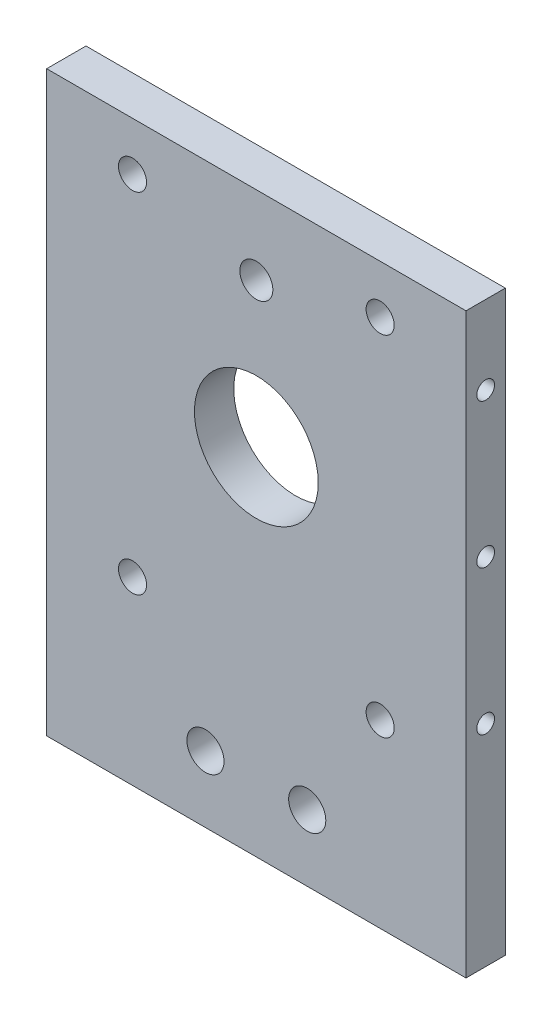
SolidWorks part; units mm, degrees
ref_plane "Alzado" through (0, 0, 0) normal (0, 0, 1) x (1, 0, 0)
ref_plane "Planta" through (0, 0, 0) normal (0, 1, 0) x (1, 0, 0)
ref_plane "Vista lateral" through (0, 0, 0) normal (1, 0, 0) x (0, 0, -1)
sketch "Croquis1" plane through (0, 0, 0) normal (0, 0, 1) x (1, 0, 0)
  line L1 (-50.8, 54) -> (50.8, 54)
  line L2 (-50.8, 54) -> (-50.8, -54)
  line L3 (-50.8, -54) -> (50.8, -54)
  line L4 (50.8, 54) -> (50.8, -54)
  line L5 (-50.8, 54) -> (50.8, -54) construction
  line L6 (-50.8, -54) -> (50.8, 54) construction
  point P0 (0, 0)
  dimension "D1" = 108
  dimension "D2" = 101.6
extrude "Saliente-Extruir1" add sketch "Croquis1" along normal blind 9.525
sketch "Croquis2" plane through (0, 0, 9.525) normal (0, 0, 1) x (1, 0, 0)
  line L0 (50.8, 0) -> (-50.8, 0) construction
  line L1 (50.8, -54) -> (50.8, 54) construction
  line L2 (-50.8, 54) -> (-50.8, -54) construction
  line L3 (-50.8, -54) -> (50.8, -54) construction
  line L4 (-42.5, 54) -> (42.5, 54) construction
  line L5 (-42.5, 54) -> (-42.5, -54) construction
  line L6 (-42.5, -54) -> (42.5, -54) construction
  line L7 (42.5, 54) -> (42.5, -54) construction
  line L8 (-42.5, 54) -> (42.5, -54) construction
  line L9 (-42.5, -54) -> (42.5, 54) construction
  line L10 (-42.5, -35.9) -> (42.5, -35.9) construction
  line L11 (-42.5, -42.25) -> (42.5, -42.25) construction
  line L12 (0, -35.9) -> (0, -54) construction
  line L13 (-30, -42.25) -> (-30, 42.25) construction
  circle A0 centre (0, 0) radius 15
  circle A1 centre (0, -42.25) radius 4 construction
  circle A2 centre (30, -42.25) radius 3.4
  circle A3 centre (-30, -42.25) radius 3.4
  circle A4 centre (30, 42.25) radius 3.4
  circle A5 centre (-30, 42.25) radius 3.4
  circle A6 centre (-30, -15.9) radius 2.5 construction
  circle A7 centre (30, -15.9) radius 2.5 construction
  point P6 (0, 0)
  dimension "D2" = 30
  dimension "D5" = 8
  dimension "D6" = 6.8
  dimension "D10" = 5
  dimension "D1" = 85
  dimension "D3" = 6.35
  dimension "D4" = 42.25
  dimension "D7" = 30
  dimension "D8" = 0
  dimension "D9" = 20
extrude "Cortar-Extruir1" cut sketch "Croquis2" against normal through all
sketch "Croquis3" plane through (-50.8, 0, 0) normal (-1, 0, 0) x (0, 0, 1)
  line L0 (4.7625, 54) -> (4.7625, -54) construction
  line L1 (9.525, 54) -> (0, 54) construction
  line L2 (9.525, -54) -> (0, -54) construction
  line L3 (0, 0) -> (9.525, 0) construction
  line L4 (9.525, 54) -> (9.525, -54) construction
  circle A0 centre (4.7625, 0) radius 2.15
  circle A1 centre (4.7625, -35) radius 2.15
  circle A2 centre (4.7625, 35) radius 2.15
  dimension "D1" = 4.3
  dimension "D2" = 4.3
  dimension "D3" = 35
extrude "Cortar-Extruir2" cut sketch "Croquis3" against normal blind 15
sketch "Croquis4" plane through (50.8, 0, 0) normal (1, 0, 0) x (0, 0, -1)
  line L0 (-4.7625, -54) -> (-4.7625, 54) construction
  line L1 (-9.525, -54) -> (0, -54) construction
  line L2 (-9.525, 54) -> (0, 54) construction
  line L3 (0, 0) -> (-9.525, 0) construction
  line L4 (0, -54) -> (0, 54) construction
  line L5 (-9.525, -54) -> (-9.525, 54) construction
  circle A0 centre (-4.7625, 0) radius 2.15
  circle A1 centre (-4.7625, -35) radius 2.15
  circle A2 centre (-4.7625, 35) radius 2.15
  dimension "D1" = 4.3
  dimension "D2" = 4.3
  dimension "D3" = 35
extrude "Cortar-Extruir3" cut sketch "Croquis4" against normal blind 15
sketch "Croquis5" plane through (0, 0, 9.525) normal (0, 0, 1) x (1, 0, 0)
  line L0 (0, 54) -> (0, 70) construction
  line L1 (50.8, 54) -> (-50.8, 54) construction
  line L2 (-50.8, -54) -> (50.8, -54) construction
  line L3 (-50.8, 86) -> (50.8, 86) construction
  line L4 (-50.8, 86) -> (-50.8, 54) construction
  line L5 (-50.8, 54) -> (50.8, 54) construction
  line L6 (50.8, 86) -> (50.8, 54) construction
  line L7 (-50.8, 86) -> (50.8, 54) construction
  line L8 (-50.8, 54) -> (50.8, 86) construction
  line L9 (0, 0) -> (50.8, 0) construction
  line L10 (50.8, -54) -> (50.8, 54) construction
  line L11 (-50.8, -54) -> (50.8, -54)
  line L12 (50.8, -86) -> (50.8, -54)
  line L13 (-50.8, -86) -> (50.8, -86)
  line L14 (-50.8, -86) -> (-50.8, -54)
  dimension "D1" = 140
extrude "Saliente-Extruir2" add sketch "Croquis5" against normal up to surface (9.525 mm away) up to face at (-26.6, 42.25, 0)
sketch "Croquis6" plane through (0, 0, 9.525) normal (0, 0, 1) x (1, 0, 0)
  line L0 (0, 0) -> (0, -86) construction
  line L1 (-50.8, -86) -> (50.8, -86) construction
  line L2 (0, 0) -> (12.329, -69.9214) construction
  circle A0 centre (0, 0) radius 71 construction
  circle A1 centre (12.329, -69.9214) radius 4.5
  circle A2 centre (-12.329, -69.9214) radius 4.5
  circle A3 centre (0, 35.0049) radius 4
  dimension "D1" = 142
  dimension "D3" = 9
  dimension "D4" = 8
  dimension "D2" = 10
extrude "Cortar-Extruir4" cut sketch "Croquis6" against normal blind 101.6
